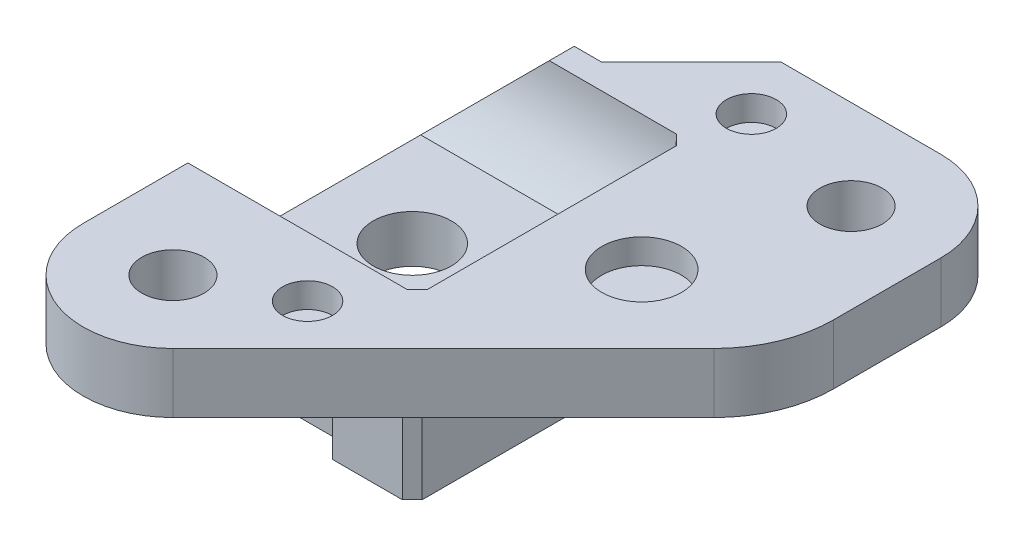
SolidWorks part; units mm, degrees
ref_plane "Front Plane" through (0, 0, 0) normal (0, 0, 1) x (1, 0, 0)
ref_plane "Top Plane" through (0, 0, 0) normal (0, 1, 0) x (1, 0, 0)
ref_plane "Right Plane" through (0, 0, 0) normal (1, 0, 0) x (0, 0, -1)
sketch "Sketch1" plane through (0, 0, 0) normal (0, 1, 0) x (1, 0, 0)
  line L0 (1, 6.5) -> (1, 7.5) construction
  line L1 (3.182, -15.182) -> (18.5, 0.136)
  line L2 (-4.5, -12) -> (-4.5, -6.5)
  line L3 (6, 12.5) -> (14, 12.5)
  line L4 (18.5, 0.136) -> (18.5, 8)
  line L5 (-4.5, -6.5) -> (8, -6.5) construction
  line L6 (8, 0) -> (0, 0) construction
  line L7 (1, 6.5) -> (8, 6.5) construction
  line L8 (8, -6.5) -> (8, 6.5) construction
  line L9 (1, 7.5) -> (6, 12.5)
  line L10 (-4.5, -6.5) -> (-4.5, 2)
  line L11 (-4.5, 2) -> (1, 7.5)
  circle A0 centre (0, -12) radius 1.5625
  circle A1 centre (14, 8) radius 1.5625
  arc A2 (18.5, 8) -> (14, 12.5) centre (14, 8) ccw
  arc A3 (3.182, -15.182) -> (-4.5, -12) centre (0, -12) cw
  dimension "D4" = 3.125
  dimension "D1" = 12
  dimension "D2" = 8
  dimension "D3" = 14
  dimension "D5" = 13
  dimension "D6" = 1
  dimension "D7" = 8
  dimension "D8" = 12.5
  dimension "D9" = 45
  dimension "D10" = 45
  dimension "D11" = 1
extrude "Boss-Extrude1" add sketch "Sketch1" along normal blind 3
sketch "Sketch2" plane through (0, 0, 0) normal (0, -1, 0) x (1, 0, 0)
  line L0 (-4.5, -2) -> (-4.5, 12) construction
  line L1 (9, -9) -> (5, -9)
  line L2 (9, -9) -> (9, 9)
  line L3 (9, 9) -> (5, 9)
  line L4 (5, -9) -> (5, -8)
  line L5 (5, -8) -> (-4.5, -8)
  line L7 (5, 8) -> (-4.5, 8)
  line L8 (-4.5, -8) -> (-4.5, 8)
  line L9 (5, 8) -> (5, 9)
  circle A0 centre (0, 0) radius 1.96
  dimension "D7" = 3.92
  dimension "D1" = 9
  dimension "D2" = 8
  dimension "D3" = 8
  dimension "D4" = 1
  dimension "D5" = 4
  dimension "D6" = 9
extrude "Boss-Extrude2" add sketch "Sketch2" along normal blind 4 and the other way up to surface (3 mm away) other way up to face at (0, 3, 13.5625)
sketch "Sketch3" plane through (-4.5, 0, 0) normal (-1, 0, 0) x (0, 0, 1)
  line L1 (-4.9212, -1.62) -> (4.9212, -1.62)
  line L4 (-6.75, 3) -> (6.75, 3)
  line L8 (-8, 3) -> (12, 3) construction
  line L9 (0, 0) -> (0, 3) construction
  arc A0 (-6.75, 3) -> (-4.9212, -1.62) centre (0, 3) ccw
  arc A1 (4.9212, -1.62) -> (6.75, 3) centre (0, 3) ccw
  point P8 (0, 0)
  dimension "D1" = 1.62
  dimension "D2" = 13.5
extrude "Cut-Extrude1" cut sketch "Sketch3" against normal blind 11.5
chamfer "Chamfer1" distance 0.5 angle 45 5 edges at (7, 0.5156, -6.2762) (7, -1.62, 0) (7, 0.5156, 6.2762) (9, -2, -9) (9, -2, 9)
sketch "Sketch5" plane through (0, 0, -8) normal (0, 0, -1) x (-1, 0, 0)
  line L0 (4.5, -1.62) -> (-0.12, 3)
  line L1 (-1.5, 3) -> (4.5, 3) construction
  line L2 (-0.12, 3) -> (4.5, 3)
  line L3 (4.5, 3) -> (4.5, -1.62)
  dimension "D1" = 45
extrude "Cut-Extrude3" cut sketch "Sketch5" against normal blind 4.7625
fillet "Fillet1" radius 6 1 edges at (18.5, 1.5, -0.136)
sketch "Sketch6" plane through (0, 3, 0) normal (0, 1, 0) x (1, 0, 0)
  circle A0 centre (11.5, 0) radius 2
  circle A1 centre (4.5, -9.75) radius 1.25
  circle A2 centre (7.5, 9.5) radius 1.25
  dimension "D1" = 2.5
  dimension "D2" = 4
  dimension "D3" = 11.5
  dimension "D4" = 4.5
  dimension "D5" = 9.75
  dimension "D6" = 9.5
  dimension "D7" = 7.5
extrude "Cut-Extrude4" cut sketch "Sketch6" against normal blind 1.25
